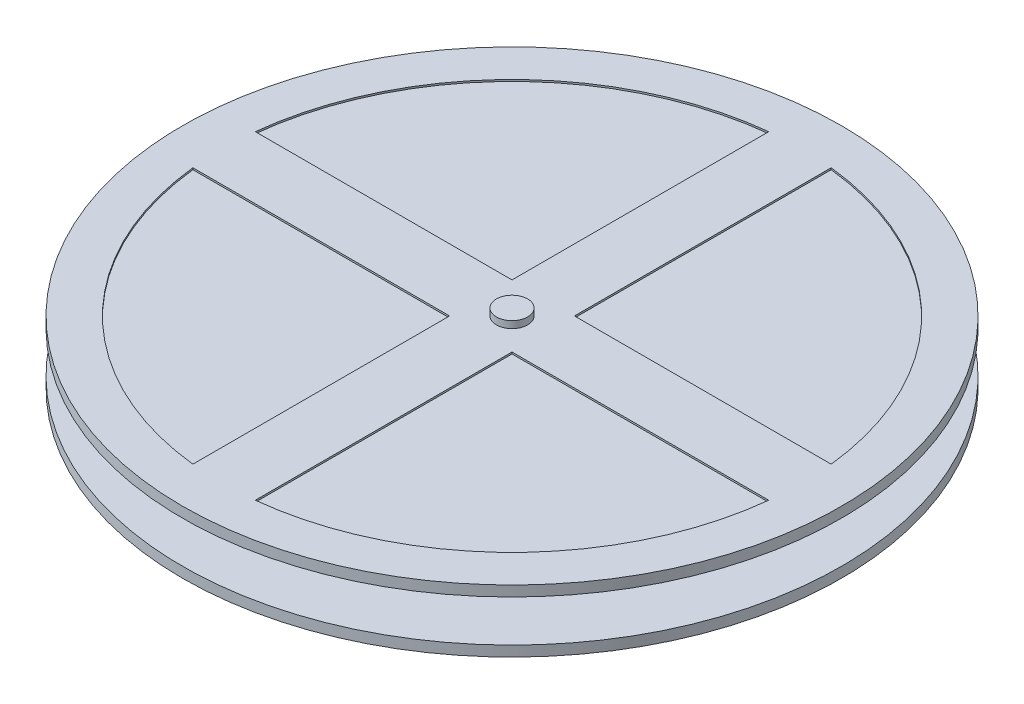
SolidWorks part; units mm, degrees
ref_plane "Front" through (0, 0, 0) normal (0, 0, 1) x (1, 0, 0)
ref_plane "Top" through (0, 0, 0) normal (0, 1, 0) x (1, 0, 0)
ref_plane "Right" through (0, 0, 0) normal (1, 0, 0) x (0, 0, -1)
sketch "Sketch2" plane through (0, 0, 0) normal (0, 0, 1) x (1, 0, 0)
  line L0 (-26, -1) -> (-26, 9)
  line L1 (-39, -10.5) -> (39, -10.5)
  line L2 (-39, -10.5) -> (-39, 10.5)
  line L3 (-39, 10.5) -> (39, 10.5)
  line L4 (39, -10.5) -> (39, 10.5)
  line L5 (-39, -10.5) -> (39, 10.5) construction
  line L6 (-39, 10.5) -> (39, -10.5) construction
  line L7 (-36, -1) -> (-26, -1)
  line L8 (-36, -1) -> (-36, 9)
  line L9 (-36, 9) -> (-26, 9)
  line L10 (36, -1) -> (36, 9)
  line L11 (26, -1) -> (26, 9)
  line L12 (26, 9) -> (36, 9)
  line L14 (26, -1) -> (36, -1)
  point P0 (0, 0)
  dimension "D1" = 78
  dimension "D2" = 21
  dimension "D3" = 10
  dimension "D4" = 10
  dimension "D5" = 1.5
  dimension "D6" = 3
  dimension "D7" = 3
  dimension "D8" = 10
extrude "Boss-Extrude1" add sketch "Sketch2" along normal blind 50
chamfer "Chamfer1" distance 2.5 angle 45 2 edges at (39, -10.5, 25) (-39, -10.5, 25)
chamfer "Chamfer2" distance 0.5 angle 45 2 edges at (39, 10.5, 25) (-39, 10.5, 25)
sketch "Sketch3" plane through (0, 10.5, 0) normal (0, 1, 0) x (1, 0, 0)
  line L0 (-38.5, -25) -> (38.5, -25) construction
  line L1 (-38.5, 0) -> (-38.5, -50) construction
  line L2 (38.5, -50) -> (38.5, 0) construction
  circle A0 centre (0, -25) radius 4.5
  dimension "D1" = 9
extrude "Boss-Extrude2" add sketch "Sketch3" along normal blind 25
sketch "Sketch4" plane through (0, 10.5, 0) normal (0, 1, 0) x (1, 0, 0)
  circle A0 centre (0, -25) radius 95
  circle A1 centre (0, -25) radius 4.5
  circle A2 centre (0, -25) radius 4.5
  dimension "D2" = 190
  dimension "D1" = 0
extrude "Boss-Extrude3" add sketch "Sketch4" along normal blind 18 from offset 5
sketch "Sketch5" plane through (0, 0, 0) normal (1, 0, 0) x (0, 0, -1)
  line L0 (70, 15.5) -> (70, 33.5) construction
  line L1 (70, 30.5) -> (-16, 30.5)
  line L2 (70, 30.5) -> (70, 18.5)
  line L3 (70, 18.5) -> (-16, 18.5)
  line L4 (-16, 30.5) -> (-16, 18.5)
  line L5 (70, 33.5) -> (-120, 33.5) construction
  line L6 (-120, 15.5) -> (70, 15.5) construction
  line L7 (0, 10) -> (-50, 10) construction
  line L8 (-25, 10.5) -> (-25, 35.5) construction
  line L9 (-50, 10.5) -> (0, 10.5) construction
  line L10 (-20.5, 35.5) -> (-29.5, 35.5) construction
  point P12 (-25, 10)
  dimension "D1" = 3
  dimension "D2" = 3
  dimension "D3" = 9
revolve "Cut-Revolve1" cut sketch "Sketch5" angle 360 about L8
sketch "Sketch6" plane through (0, 33.5, 0) normal (0, 1, 0) x (1, 0, 0)
  line L0 (0, 70) -> (0, -120) construction
  line L1 (-95, -25) -> (95, -25) construction
  line L2 (9, 58.0066) -> (9, -16)
  line L3 (9, -16) -> (83.0066, -16)
  circle A0 centre (0, -25) radius 95 construction
  arc A1 (83.0066, -16) -> (9, 58.0066) centre (0, -25) ccw
  dimension "D1" = 9
extrude "Cut-Extrude1" cut sketch "Sketch6" against normal blind 0.5
pattern_circular "CirPattern1" count 4 over 360 about axis through (0, 0, 25) along (0, 1, 0) of "Cut-Extrude1"
